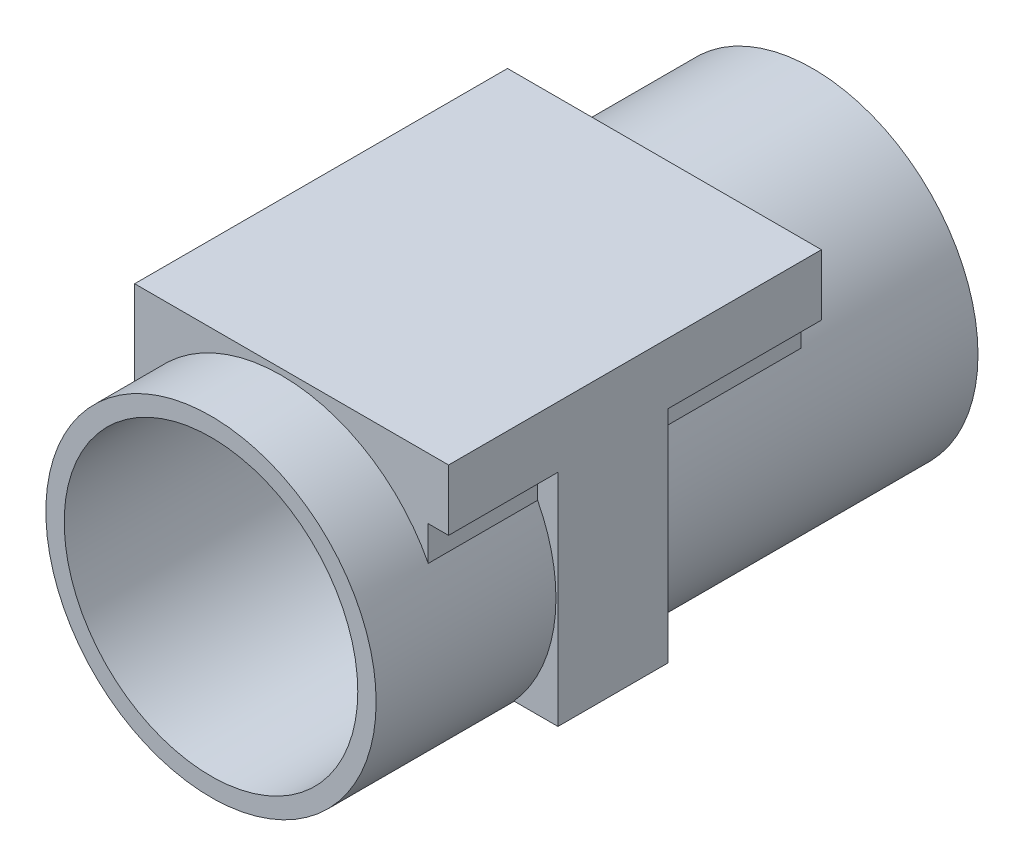
SolidWorks part; units mm, degrees
ref_plane "Front Plane" through (0, 0, 0) normal (0, 0, 1) x (1, 0, 0)
ref_plane "Top Plane" through (0, 0, 0) normal (0, 1, 0) x (1, 0, 0)
ref_plane "Right Plane" through (0, 0, 0) normal (1, 0, 0) x (0, 0, -1)
sketch "Sketch1" plane through (0, 0, 0) normal (1, 0, 0) x (0, 0, -1)
  line L6 (0, 0) -> (2, 0)
  line L7 (2, 0) -> (2, -22.5)
  line L8 (2, -22.5) -> (-80, -22.5)
  line L9 (-80, -22.5) -> (-80, -20)
  line L10 (-80, -20) -> (0, -20)
  line L11 (0, -20) -> (0, 0)
  dimension "D1" = 2
  dimension "D2" = 20
  dimension "D3" = 80
  dimension "D4" = 2.5
revolve "Revolve1" add sketch "Sketch1" angle 360 about L6
ref_plane "Plane1" through (0, 0, 48) normal (0, 0, -1) x (-1, 0, 0)
sketch "Sketch3" plane through (0, 0, 48) normal (0, 0, -1) x (-1, 0, 0)
  line L0 (-16.7705, 15) -> (-22.7705, 15)
  line L1 (-22.7705, 15) -> (-22.7705, -15)
  line L2 (-22.7705, -15) -> (-16.7705, -15)
  circle A0 centre (0, 0) radius 22.5 construction
  arc A1 (-16.7705, 15) -> (-16.7705, -15) centre (0, 0) ccw
  point P7 (-22.5, 0)
  point P10 (-22.7705, 0)
  dimension "D1" = 6
  dimension "D2" = 30
extrude "Boss-Extrude1" add sketch "Sketch3" along normal blind 7.5 and the other way blind 7.5
sketch "Sketch4" plane through (0, 0, 48) normal (0, 0, -1) x (-1, 0, 0)
  line L0 (20, 10.3078) -> (20, 23.3078)
  line L1 (20, 23.3078) -> (-20, 23.3078)
  line L2 (-20, 23.3078) -> (-20, 10.3078)
  line L3 (-22.7705, 15) -> (-22.7705, 23.3078)
  line L4 (-22.7705, 23.3078) -> (-20, 23.3078)
  line L5 (-19.7705, 15) -> (-22.7705, 15)
  line L6 (-16.7705, 15) -> (-22.7705, 15) construction
  circle A0 centre (0, 0) radius 22.5 construction
  arc A1 (20, 10.3078) -> (-20, 10.3078) centre (0, 0) ccw
  point P7 (0, 22.5)
  point P8 (0, 23.3078)
  dimension "D1" = 40
  dimension "D2" = 13
extrude "Boss-Extrude2" add sketch "Sketch4" along normal blind 28.4 and the other way blind 22.4
